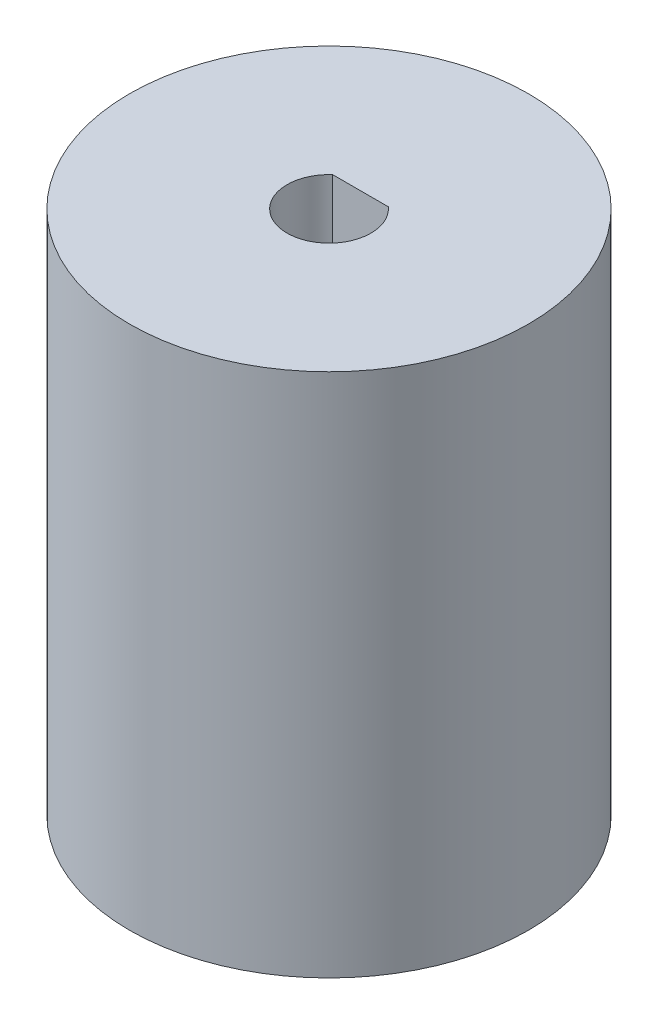
SolidWorks part; units mm, degrees
ref_plane "Plan de face" through (0, 0, 0) normal (0, 0, 1) x (1, 0, 0)
ref_plane "Plan de dessus" through (0, 0, 0) normal (0, 1, 0) x (1, 0, 0)
ref_plane "Plan de droite" through (0, 0, 0) normal (1, 0, 0) x (0, 0, -1)
sketch "Esquisse1" plane through (0, 0, 0) normal (0, 0, 1) x (1, 0, 0)
  line L0 (0, 0) -> (0, -16.5652) construction
  line L1 (-4, 0) -> (-4, 18)
  line L2 (-4, 18) -> (-2, 18)
  line L3 (-2, 18) -> (-2, 25)
  line L4 (-2, 25) -> (-9.5, 25)
  line L5 (-9.5, 25) -> (-9.5, 0)
  line L6 (-9.5, 0) -> (-4, 0)
  dimension "D1" = 2
  dimension "D2" = 4
  dimension "D3" = 9.5
  dimension "D4" = 25
  dimension "D5" = 7
revolve "Révolution1" add sketch "Esquisse1" angle 360 about L0
sketch "Esquisse2" plane through (0, 25, 0) normal (0, 1, 0) x (1, 0, 0)
  line L0 (-1.3229, 1.5) -> (1.3229, 1.5)
  arc A0 (1.3229, 1.5) -> (-1.3229, 1.5) centre (0, 0) ccw
  circle A1 centre (0, 0) radius 2 construction
  dimension "D1" = 1.5
extrude "Boss.-Extru.1" add sketch "Esquisse2" against normal up to surface (7 mm away) up to face at (-2, 18, 0)
